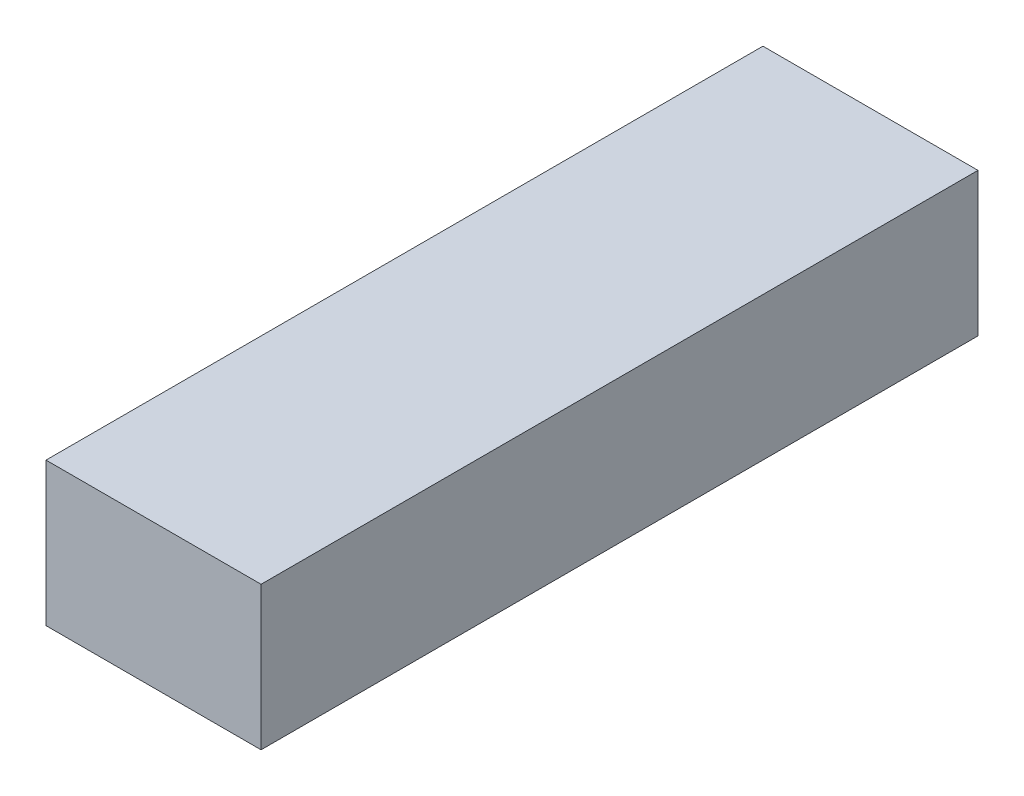
SolidWorks part; units mm, degrees
ref_plane "Спереди" through (0, 0, 0) normal (0, 0, 1) x (1, 0, 0)
ref_plane "Сверху" through (0, 0, 0) normal (0, 1, 0) x (1, 0, 0)
ref_plane "Справа" through (0, 0, 0) normal (1, 0, 0) x (0, 0, -1)
sketch "Эскиз1" plane through (0, 0, 0) normal (1, 0, 0) x (0, 0, -1)
  line L1 (0, 0) -> (20, 0)
  line L2 (0, 0) -> (0, 4)
  line L3 (0, 4) -> (20, 4)
  line L4 (20, 0) -> (20, 4)
extrude "Бобышка-Вытянуть1" add sketch "Эскиз1" along normal blind 6
